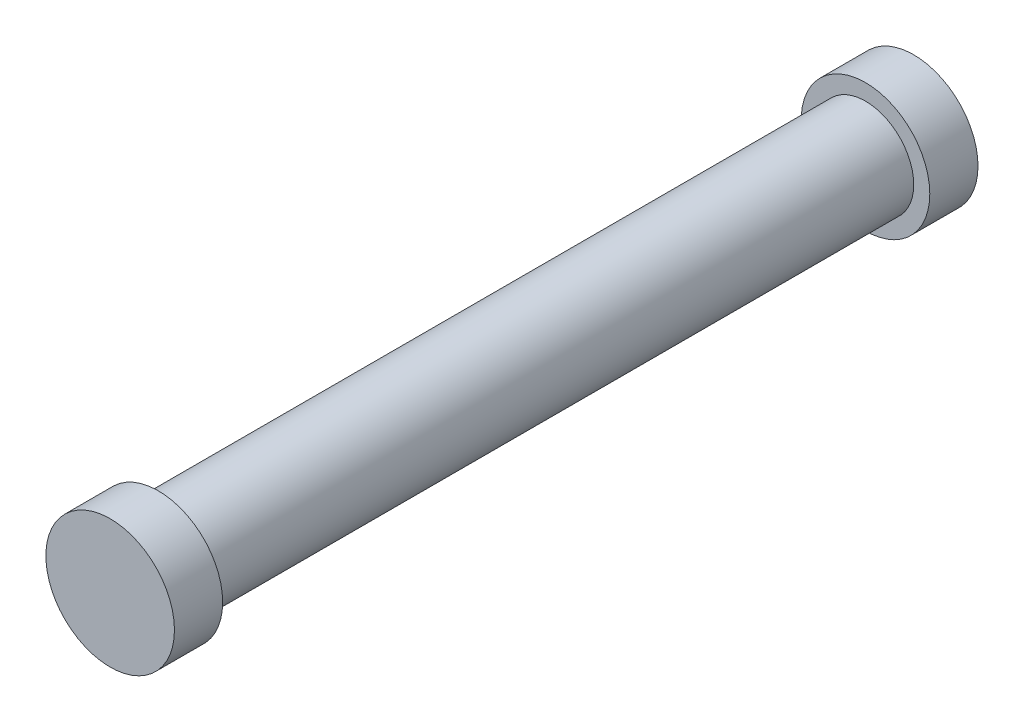
SolidWorks part; units mm, degrees
ref_plane "Front Plane" through (0, 0, 0) normal (0, 0, 1) x (1, 0, 0)
ref_plane "Top Plane" through (0, 0, 0) normal (0, 1, 0) x (1, 0, 0)
ref_plane "Right Plane" through (0, 0, 0) normal (1, 0, 0) x (0, 0, -1)
sketch "Sketch1" plane through (0, 0, 0) normal (0, 0, 1) x (1, 0, 0)
  circle A0 centre (0, 0) radius 25.4
  dimension "D1" = 50.8
extrude "Boss-Extrude1" add sketch "Sketch1" along normal blind 19.05
sketch "Sketch2" plane through (0, 0, 19.05) normal (0, 0, 1) x (1, 0, 0)
  circle A0 centre (0, 0) radius 19.05
  dimension "D1" = 38.1
extrude "Boss-Extrude2" add sketch "Sketch2" along normal blind 279.4
sketch "Sketch3" plane through (0, 0, 298.45) normal (0, 0, 1) x (1, 0, 0)
  circle A0 centre (0, 0) radius 25.4
extrude "Boss-Extrude3" add sketch "Sketch3" along normal blind 19.05
